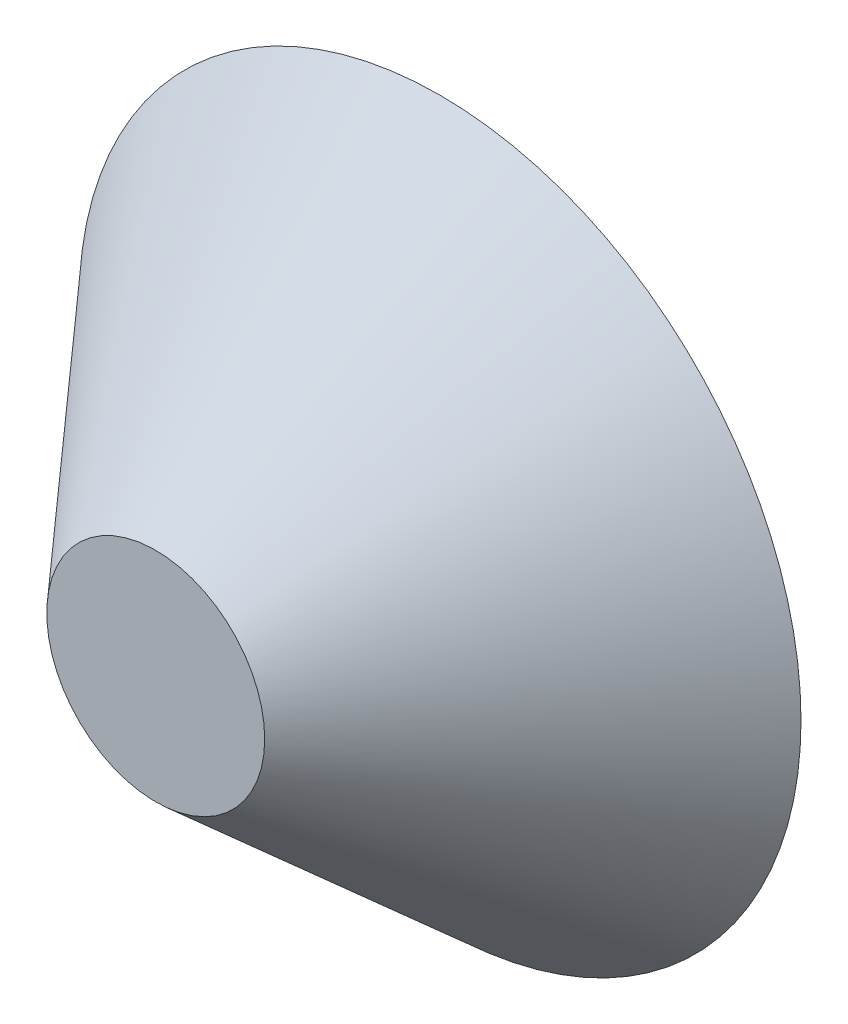
SolidWorks part; units mm, degrees
ref_plane "Front Plane" through (0, 0, 0) normal (0, 0, 1) x (1, 0, 0)
ref_plane "Top Plane" through (0, 0, 0) normal (0, 1, 0) x (1, 0, 0)
ref_plane "Right Plane" through (0, 0, 0) normal (1, 0, 0) x (0, 0, -1)
sketch "Sketch1" plane through (0, 0, 0) normal (0, 0, 1) x (1, 0, 0)
  circle A0 centre (0, 0) radius 38.1
  dimension "D1" = 76.2
ref_plane "Plane1" through (0, 0, 30) normal (0, 0, 1) x (1, 0, 0)
sketch "Sketch2" plane through (0, 0, 30) normal (0, 0, 1) x (1, 0, 0)
  circle A0 centre (0, 0) radius 11.5
  dimension "D1" = 23
loft "Loft1" add profiles "Sketch1", "Sketch2"
